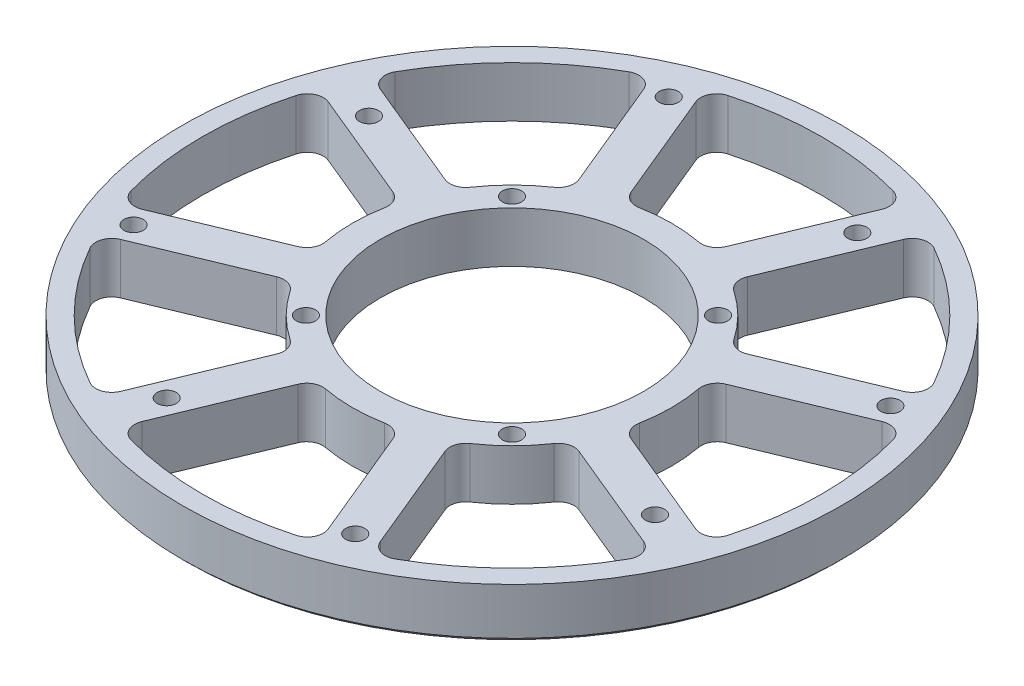
SolidWorks part; units mm, degrees
material "6061-T6 (SS)"
ref_plane "Front Plane" through (0, 0, 0) normal (0, 0, 1) x (1, 0, 0)
ref_plane "Top Plane" through (0, 0, 0) normal (0, 1, 0) x (1, 0, 0)
ref_plane "Right Plane" through (0, 0, 0) normal (1, 0, 0) x (0, 0, -1)
sketch "Sketch2" plane through (0, 0, 0) normal (1, 0, 0) x (0, 0, -1)
  line L0 (0, 0) -> (-82.55, 0)
  line L1 (-82.55, 0) -> (-82.55, 12.7)
  line L2 (-82.55, 12.7) -> (0, 12.7)
  line L5 (0, 12.7) -> (0, 0)
  dimension "D1" = 82.55
  dimension "D2" = 12.7
ref_axis "Axis1" through (0, -0.635, 0) along (0, 1, 0)
revolve "Revolve1" add sketch "Sketch2" angle 360 about axis through (0, -0.635, 0) along (0, 1, 0)
hole_wizard "#12 (0.189) Diameter Hole1" positions "Sketch6" profile "Sketch7" hole size "#12" standard "ANSI Inch" end condition through all
sketch "Sketch6" plane through (0, 12.7, 0) normal (0, 1, 0) x (1, 0, 0)
  line L0 (0, 0) -> (-53.438, 129.0108) construction
  line L2 (0, 0) -> (0, 109.0908) construction
  line L3 (0, 0) -> (-76.2663, 31.5905) construction
  line L4 (0, 0) -> (-68.4315, 68.4315) construction
  circle A0 centre (0, 0) radius 82.55 construction
  point P0 (-27.7637, 67.0275)
  point P18 (-61.1608, 25.3336)
  point P27 (-25.8094, 25.8094)
  dimension "D1" = 22.5
  dimension "D2" = 72.55
  dimension "D3" = 45
  dimension "D4" = 66.2
  dimension "D6" = 22.5
  dimension "D5" = 36.5
sketch "Sketch7" plane through (-27.7637, 12.7, -67.0275) normal (1, 0, 0) x (0, 0, 1)
  line L0 (0, 0) -> (0, 12.7)
  line L1 (0, 12.7) -> (2.4003, 12.7)
  line L2 (2.4003, 12.7) -> (2.4003, 0)
  line L5 (2.4003, 0) -> (0, 0)
  line L11 (0, -6.35) -> (0, 107.95) construction
  dimension "Thru Hole Dia." = 4.8006
  dimension "Thru Hole Depth" = 12.7
pattern_circular "CirPattern3" count 4 over 360 about axis through (0, 0, 0) along (0, 1, 0) of "#12 (0.189) Diameter Hole1"
sketch "Sketch8" plane through (0, 12.7, 0) normal (0, 1, 0) x (1, 0, 0)
  line L4 (0, 0) -> (0, 93.9995) construction
  line L5 (0, 0) -> (113.8372, 0) construction
  line L6 (-10.5679, 38.5787) -> (-24.996, 73.4112)
  line L7 (10.5679, 38.5787) -> (24.996, 73.4112)
  line L8 (0, 0) -> (-27.7637, 67.0275) construction
  arc A0 (-10.5679, 38.5787) -> (10.5679, 38.5787) centre (0, 0) cw
  arc A1 (-24.996, 73.4112) -> (24.996, 73.4112) centre (0, 0) cw
  circle A2 centre (0, 0) radius 82.55 construction
  dimension "D1" = 40
  dimension "D2" = 5
  dimension "D3" = 5
extrude "Cut-Extrude1" cut sketch "Sketch8" against normal through all
fillet "Fillet1" radius 4 4 edges at (10.5679, 6.35, -38.5787) (24.996, 6.35, -73.4112) (-10.5679, 6.35, -38.5787) (-24.996, 6.35, -73.4112)
pattern_circular "CirPattern4" count 8 over 360 about axis through (0, 0, 0) along (0, 1, 0) of "Cut-Extrude1", "Fillet1"
chamfer "Chamfer2" distance 1 angle 45 1 edges at (0, 0, -82.55)
sketch "Sketch9" plane through (0, 12.7, 0) normal (0, 1, 0) x (1, 0, 0)
  circle A0 centre (0, 0) radius 33
  dimension "D1" = 66
extrude "Cut-Extrude2" cut sketch "Sketch9" against normal through all
equation "\"TubeDiameter\" = 6.500in"
equation "\"D1@Sketch2\"=\"TubeDiameter\"/2"
equation "\"D2@Sketch6\"=\"TubeDiameter\"/2-10mm"
